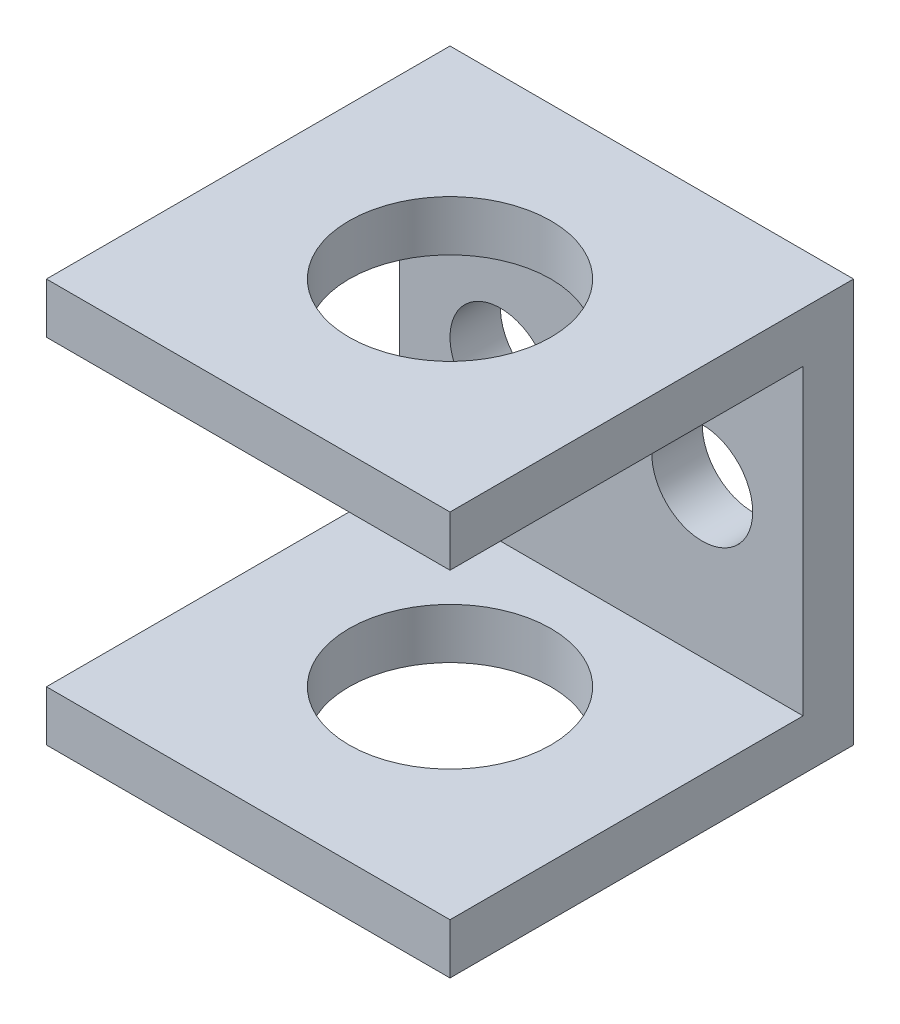
SolidWorks part; units mm, degrees
ref_plane "Front Plane" through (0, 0, 0) normal (0, 0, 1) x (1, 0, 0)
ref_plane "Top Plane" through (0, 0, 0) normal (0, 1, 0) x (1, 0, 0)
ref_plane "Right Plane" through (0, 0, 0) normal (1, 0, 0) x (0, 0, -1)
sketch "Sketch1" plane through (0, 0, 0) normal (0, 0, 1) x (1, 0, 0)
  line L1 (0, 0) -> (20, 0)
  line L2 (0, 0) -> (0, 20)
  line L3 (0, 20) -> (20, 20)
  line L4 (20, 0) -> (20, 20)
  dimension "D1" = 20
  dimension "D2" = 20
extrude "Boss-Extrude1" add sketch "Sketch1" along normal blind 20
sketch "Sketch2" plane through (0, 0, 20) normal (0, 0, 1) x (1, 0, 0)
  line L0 (0, 20) -> (0, 0) construction
  line L1 (0, 17.5) -> (20, 17.5)
  line L2 (0, 17.5) -> (0, 2.5)
  line L3 (0, 2.5) -> (20, 2.5)
  line L4 (20, 17.5) -> (20, 2.5)
  line L5 (20, 20) -> (0, 20) construction
  dimension "D1" = 2.5
  dimension "D2" = 0
  dimension "D3" = 2.5
  dimension "D4" = 20
extrude "Cut-Extrude1" cut sketch "Sketch2" against normal blind 17.5
sketch "Sketch3" plane through (0, 20, 0) normal (0, 1, 0) x (1, 0, 0)
  circle A0 centre (10, -10) radius 5
  dimension "D1" = 10
  dimension "D2" = 10
  dimension "D3" = 10
extrude "Cut-Extrude2" cut sketch "Sketch3" against normal through all
sketch "Sketch4" plane through (0, 0, 2.5) normal (0, 0, 1) x (1, 0, 0)
  line L0 (5, 10) -> (15, 10) construction
  circle A0 centre (15, 10) radius 2.5
  circle A1 centre (5, 10) radius 2.5
  dimension "D2" = 5
  dimension "D3" = 5
  dimension "D1" = 10
  dimension "D4" = 5
  dimension "D5" = 10
extrude "Cut-Extrude3" cut sketch "Sketch4" against normal through all
